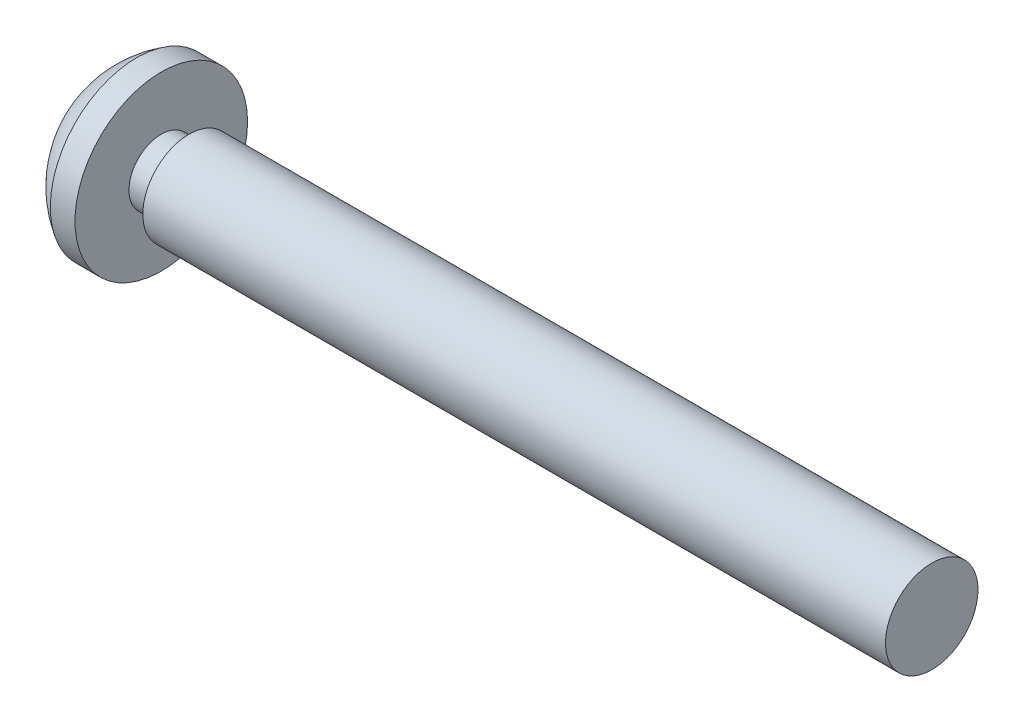
SolidWorks part; units mm, degrees
ref_plane "前视基准面" through (0, 0, 0) normal (0, 0, 1) x (1, 0, 0)
ref_plane "上视基准面" through (0, 0, 0) normal (0, 1, 0) x (1, 0, 0)
ref_plane "右视基准面" through (0, 0, 0) normal (1, 0, 0) x (0, 0, -1)
sketch "草图2" plane through (0, 0, 0) normal (0, 0, 1) x (1, 0, 0)
  line L0 (0, 0) -> (0, 1.5)
  line L1 (0, 1.5) -> (-24.1, 1.5)
  line L2 (-24.1, 1.5) -> (-24.1, 1.05)
  line L3 (-24.1, 1.05) -> (-25, 1.05)
  line L4 (-25, 1.05) -> (-25, 2.8)
  line L5 (-25, 2.8) -> (-25.8, 2.8)
  line L6 (0, 0) -> (-32.6437, 0) construction
  line L7 (0, 0) -> (-27.4, 0)
  arc A0 (-25.8, 2.8) -> (-27.4, 0) centre (-24.15, 0) ccw
  dimension "D1" = 3
  dimension "D2" = 25
  dimension "D3" = 0.8
  dimension "D4" = 2.4
  dimension "D5" = 5.6
  dimension "D8" = 0.9
  dimension "D9" = 0.45
revolve "旋转1" add sketch "草图2" angle 360 about L6
cosmetic thread "装饰螺纹线1" parameters "D2"=2.15
ref_plane "基准面1" through (-27.4, 0, 0) normal (1, 0, 0) x (0, 0, -1)
sketch "草图3" plane through (-27.4, 0, 0) normal (1, 0, 0) x (0, 0, -1)
  line L0 (0, 1.8) -> (0, -1.8) construction
  line L1 (0.375, 1.8) -> (-0.375, 1.8)
  line L2 (0.375, 1.8) -> (0.375, 0.675)
  line L3 (0.375, -1.8) -> (-0.375, -1.8)
  line L4 (-0.375, 1.8) -> (-0.375, 0.675)
  line L5 (-1.8, 0) -> (1.8, 0) construction
  line L6 (1.8, 0.375) -> (0.675, 0.375)
  line L7 (1.8, 0.375) -> (1.8, -0.375)
  line L8 (1.8, -0.375) -> (0.675, -0.375)
  line L9 (-1.8, 0.375) -> (-1.8, -0.375)
  line L10 (0.375, -0.675) -> (0.375, -1.8)
  line L11 (-0.675, 0.375) -> (-1.8, 0.375)
  line L12 (-0.375, -0.675) -> (-0.375, -1.8)
  line L13 (-0.675, -0.375) -> (-1.8, -0.375)
  arc A0 (-0.375, -0.675) -> (-0.675, -0.375) centre (-0.675, -0.675) ccw
  arc A1 (0.375, -0.675) -> (0.675, -0.375) centre (0.675, -0.675) cw
  arc A2 (0.675, 0.375) -> (0.375, 0.675) centre (0.675, 0.675) cw
  arc A3 (-0.375, 0.675) -> (-0.675, 0.375) centre (-0.675, 0.675) cw
  point P26 (0, 0)
  dimension "D3" = 0.3
  dimension "D1" = 0.75
  dimension "D2" = 3.6
extrude "切除-拉伸5" cut sketch "草图3" along normal blind 1.2
